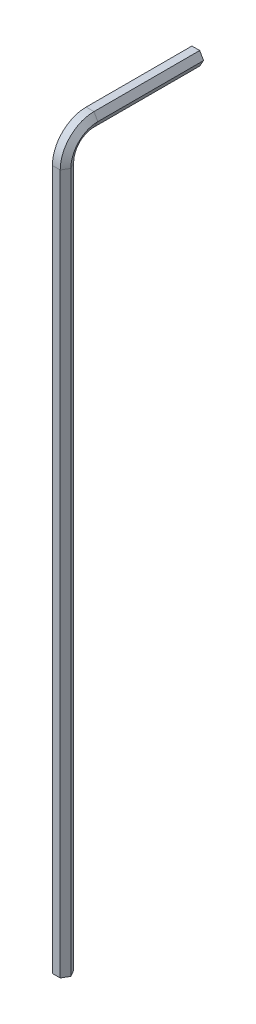
SolidWorks part; units mm, degrees
ref_plane "Front Plane" through (0, 0, 0) normal (0, 0, 1) x (1, 0, 0)
ref_plane "Top Plane" through (0, 0, 0) normal (0, 1, 0) x (1, 0, 0)
ref_plane "Right Plane" through (0, 0, 0) normal (1, 0, 0) x (0, 0, -1)
sketch "Sketch1" plane through (0, 0, 0) normal (0, 1, 0) x (1, 0, 0)
  line L1 (0.866, 0) -> (0.433, 0.75)
  line L2 (0.433, 0.75) -> (-0.433, 0.75)
  line L3 (-0.433, 0.75) -> (-0.866, 0)
  line L4 (-0.866, 0) -> (-0.433, -0.75)
  line L5 (-0.433, -0.75) -> (0.433, -0.75)
  line L6 (0.433, -0.75) -> (0.866, 0)
  circle A0 centre (0, 0) radius 0.75 construction
  dimension "D1" = 1.5
sketch "Sketch2" plane through (0, 0, 0) normal (1, 0, 0) x (0, 0, -1)
  line L0 (0, 0) -> (0, 77.75)
  line L1 (3, 80.75) -> (14.75, 80.75)
  line L3 (0.75, 0) -> (0.75, 77.75) construction
  line L4 (3, 80) -> (14.75, 80) construction
  arc A0 (0, 77.75) -> (3, 80.75) centre (3, 77.75) cw
  arc A1 (0.75, 77.75) -> (3, 80) centre (3, 77.75) cw construction
  dimension "D3" = 3
  dimension "D1" = 14
  dimension "D2" = 80
  dimension "D4" = 0.75
sweep "Sweep1" add profiles "Sketch1" path "Sketch2"
